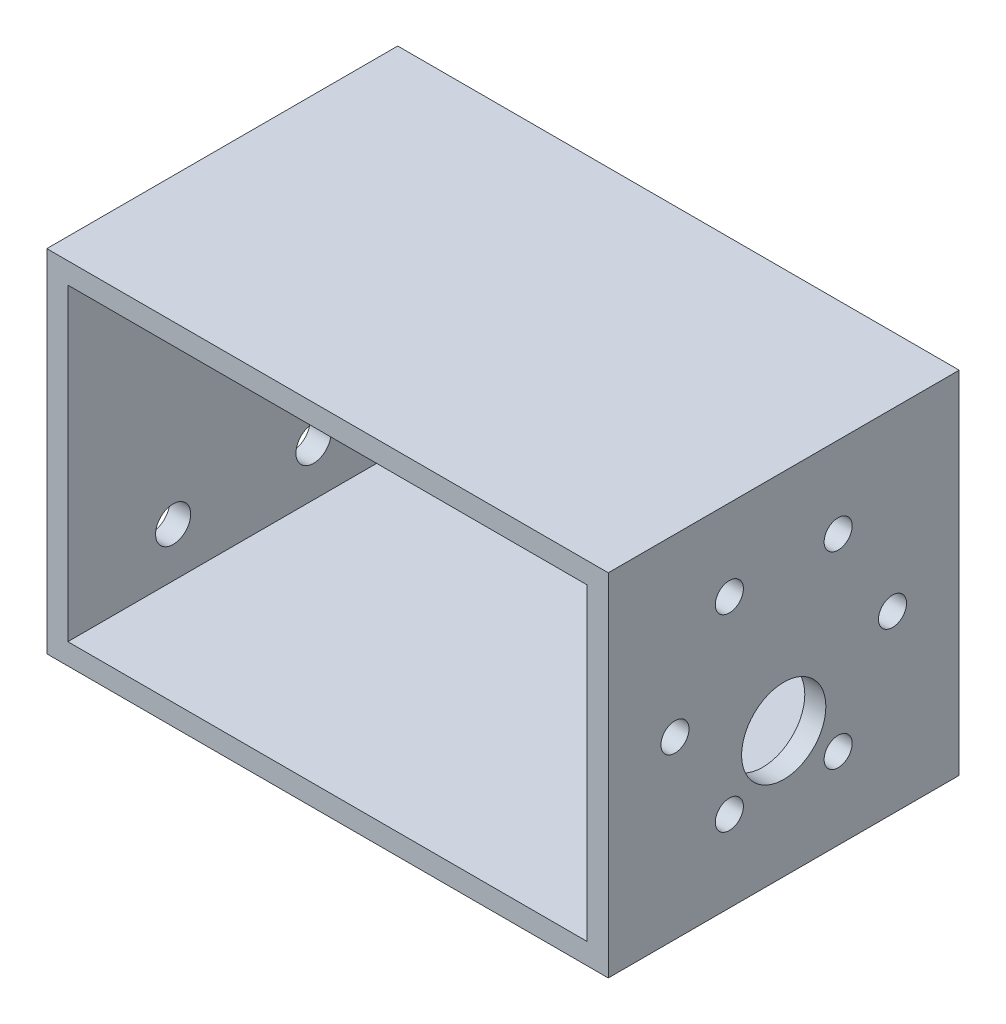
SolidWorks part; units mm, degrees
material "1060 Alloy"
ref_plane "Front" through (0, 0, 0) normal (0, 0, 1) x (1, 0, 0)
ref_plane "Top" through (0, 0, 0) normal (0, 1, 0) x (1, 0, 0)
ref_plane "Right" through (0, 0, 0) normal (1, 0, 0) x (0, 0, -1)
sketch "Sketch1" plane through (0, 0, 0) normal (0, 0, -1) x (1, 0, 0)
  line L0 (3, 3) -> (77, 3)
  line L1 (0, 0) -> (80, 0)
  line L2 (0, 0) -> (0, 50)
  line L3 (0, 50) -> (80, 50)
  line L4 (80, 0) -> (80, 50)
  line L5 (77, 3) -> (77, 47)
  line L6 (3, 47) -> (77, 47)
  line L7 (3, 3) -> (3, 47)
  dimension "D1" = 80
  dimension "D2" = 50
  dimension "D3" = 3
extrude "Boss-Extrude1" add sketch "Sketch1" along normal blind 50
sketch "Sketch2" plane through (80, 0, 0) normal (1, 0, 0) x (0, 0, -1)
  line L2 (0, 0) -> (0, -50) construction
  line L3 (50, 0) -> (0, 0) construction
  circle A0 centre (25, -25) radius 15.5 construction
  circle A1 centre (9.5, -25) radius 2
  circle A2 centre (17.25, -38.4234) radius 2
  circle A3 centre (32.75, -38.4234) radius 2
  circle A4 centre (40.5, -25) radius 2
  circle A5 centre (32.75, -11.5766) radius 2
  circle A6 centre (17.25, -11.5766) radius 2
  circle A7 centre (25, -32) radius 6
  point P4 (0, -25)
  point P21 (25, -25)
  dimension "D3" = 31
  dimension "D4" = 4
  dimension "D6" = 12
  dimension "D1" = 25
  dimension "D2" = 25
  dimension "D7" = 7
  dimension "D5" = 6
extrude "Cut-Extrude1" cut sketch "Sketch2" against normal up to surface (3 mm away) up to face at (77, -25, -25)
sketch "Sketch3" plane through (3, 0, 0) normal (1, 0, 0) x (0, 0, -1)
  line L2 (50, -50) -> (0, -50) construction
  line L3 (50, -50) -> (50, 0) construction
  circle A0 centre (15, -40) radius 2.5
  circle A1 centre (15, -10) radius 2.5
  circle A2 centre (35, -10) radius 2.5
  circle A4 centre (35, -40) radius 2.5
  dimension "D2" = 2
  dimension "D3" = 2
  dimension "D10" = 5
  dimension "D11" = 10
  dimension "D12" = 15
extrude "Cut-Extrude2" cut sketch "Sketch3" against normal up to next
